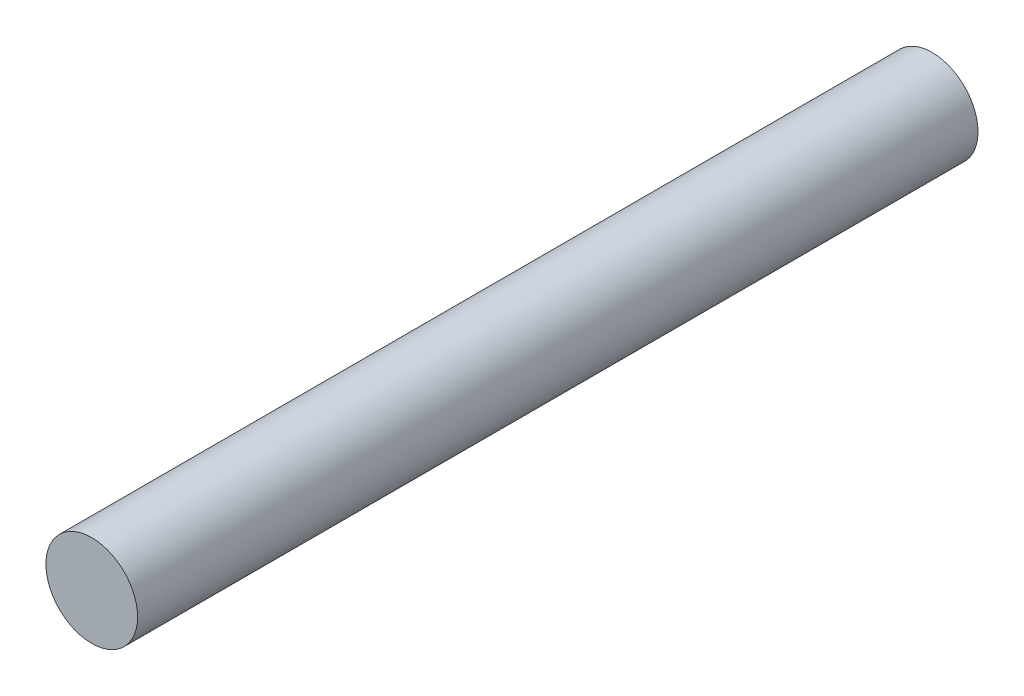
SolidWorks part; units mm, degrees
material "1060 Alloy"
ref_plane "Front Plane" through (0, 0, 0) normal (0, 0, 1) x (1, 0, 0)
ref_plane "Top Plane" through (0, 0, 0) normal (0, 1, 0) x (1, 0, 0)
ref_plane "Right Plane" through (0, 0, 0) normal (1, 0, 0) x (0, 0, -1)
sketch "Sketch1" plane through (0, 0, 0) normal (0, 0, 1) x (1, 0, 0)
  circle A0 centre (0, 0) radius 3
  dimension "D1" = 6
extrude "Boss-Extrude1" add sketch "Sketch1" along normal blind 55
